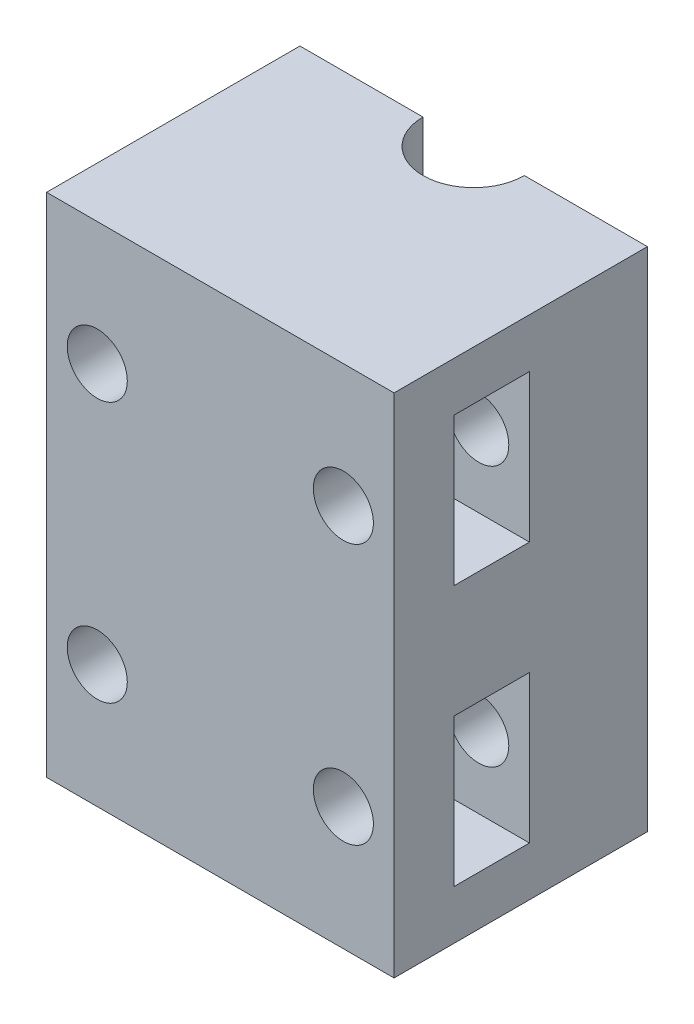
SolidWorks part; units mm, degrees
ref_plane "Спереди" through (0, 0, 0) normal (0, 0, 1) x (1, 0, 0)
ref_plane "Сверху" through (0, 0, 0) normal (0, 1, 0) x (1, 0, 0)
ref_plane "Справа" through (0, 0, 0) normal (1, 0, 0) x (0, 0, -1)
sketch "Sketch1" plane through (0, 0, 0) normal (0, 1, 0) x (1, 0, 0)
  line L1 (24, -17.5) -> (-24, -17.5)
  line L2 (24, -17.5) -> (24, 17.5)
  line L3 (24, 17.5) -> (-24, 17.5)
  line L4 (-24, -17.5) -> (-24, 17.5)
  line L5 (24, -17.5) -> (-24, 17.5) construction
  line L6 (24, 17.5) -> (-24, -17.5) construction
  point P0 (0, 0)
  dimension "D1" = 48
  dimension "D2" = 35
extrude "Boss-Extrude1" add sketch "Sketch1" along normal blind 70
sketch "Sketch2" plane through (24, 0, 0) normal (1, 0, 0) x (0, 0, -1)
  line L0 (-17.5, 35) -> (17.5, 35) construction
  line L1 (-17.5, 70) -> (-17.5, 0) construction
  line L2 (17.5, 70) -> (17.5, 0) construction
  line L3 (-4, 35) -> (-4, 70) construction
  line L4 (-9.2, 24.8) -> (1.2, 24.8) construction
  line L5 (-9.2, 24.8) -> (-9.2, 45.2) construction
  line L6 (-9.2, 45.2) -> (1.2, 45.2) construction
  line L7 (1.2, 24.8) -> (1.2, 45.2) construction
  line L8 (-9.2, 24.8) -> (1.2, 45.2) construction
  line L9 (-9.2, 45.2) -> (1.2, 24.8) construction
  line L10 (-17.5, 70) -> (17.5, 70) construction
  line L11 (-4, 35) -> (-4, 0) construction
  line L12 (-17.5, 0) -> (17.5, 0) construction
  line L13 (-5.7606, 42.8) -> (-5.7606, 27.2) construction
  line L14 (1.2, 42.8) -> (-9.2, 42.8)
  line L15 (1.2, 42.8) -> (1.2, 63.2)
  line L16 (1.2, 63.2) -> (-9.2, 63.2)
  line L17 (-9.2, 42.8) -> (-9.2, 63.2)
  line L18 (1.2, 42.8) -> (-9.2, 63.2) construction
  line L19 (1.2, 63.2) -> (-9.2, 42.8) construction
  line L20 (1.2, 6.8) -> (-9.2, 6.8)
  line L21 (1.2, 6.8) -> (1.2, 27.2)
  line L22 (1.2, 27.2) -> (-9.2, 27.2)
  line L23 (-9.2, 6.8) -> (-9.2, 27.2)
  line L24 (1.2, 6.8) -> (-9.2, 27.2) construction
  line L25 (1.2, 27.2) -> (-9.2, 6.8) construction
  line L26 (-9.2, 53) -> (-17.5, 53) construction
  line L27 (-9.2, 17) -> (-17.5, 17) construction
  point P6 (-4, 35)
  point P15 (-4, 53)
  point P23 (-4, 17)
  point P30 (-5.7606, 35)
  dimension "D1" = 10.4
  dimension "D2" = 20.4
  dimension "D3" = 13.5
  dimension "D5" = 7.8
extrude "Cut-Extrude1" cut sketch "Sketch2" against normal offset from surface (45 mm away) 3 up to face at (-24, 35, 0)
sketch "Sketch3" plane through (0, 0, 17.5) normal (0, 0, 1) x (1, 0, 0)
  line L0 (-24, 35) -> (24, 35) construction
  line L1 (-24, 70) -> (-24, 0) construction
  line L2 (24, 70) -> (24, 0) construction
  line L3 (17, 17) -> (17, 53) construction
  line L4 (-17, 17) -> (-17, 53) construction
  line L5 (24, 53) -> (-24, 53) construction
  line L6 (24, 17) -> (-24, 17) construction
  circle A0 centre (-17, 35) radius 4.15 construction
  circle A1 centre (17, 35) radius 4.15 construction
  circle A2 centre (17, 53) radius 4.15
  circle A3 centre (-17, 53) radius 4.15
  circle A4 centre (-17, 17) radius 4.15
  circle A5 centre (17, 17) radius 4.15
  point P10 (0, 35)
  point P13 (17, 35)
  point P17 (-17, 35)
  dimension "D1" = 34
  dimension "D2" = 8.3
  dimension "D3" = 17
extrude "Cut-Extrude2" cut sketch "Sketch3" against normal through all
sketch "Sketch4" plane through (0, 70, 0) normal (0, 1, 0) x (1, 0, 0)
  line L0 (0, 17.5) -> (0, -17.5) construction
  line L1 (24, 17.5) -> (-24, 17.5) construction
  line L2 (-24, -17.5) -> (24, -17.5) construction
  arc A0 (-7, 17.5) -> (7, 17.5) centre (0, 17.5) ccw
  dimension "D1" = 7
extrude "Cut-Extrude3" cut sketch "Sketch4" against normal through all and the other way through all
